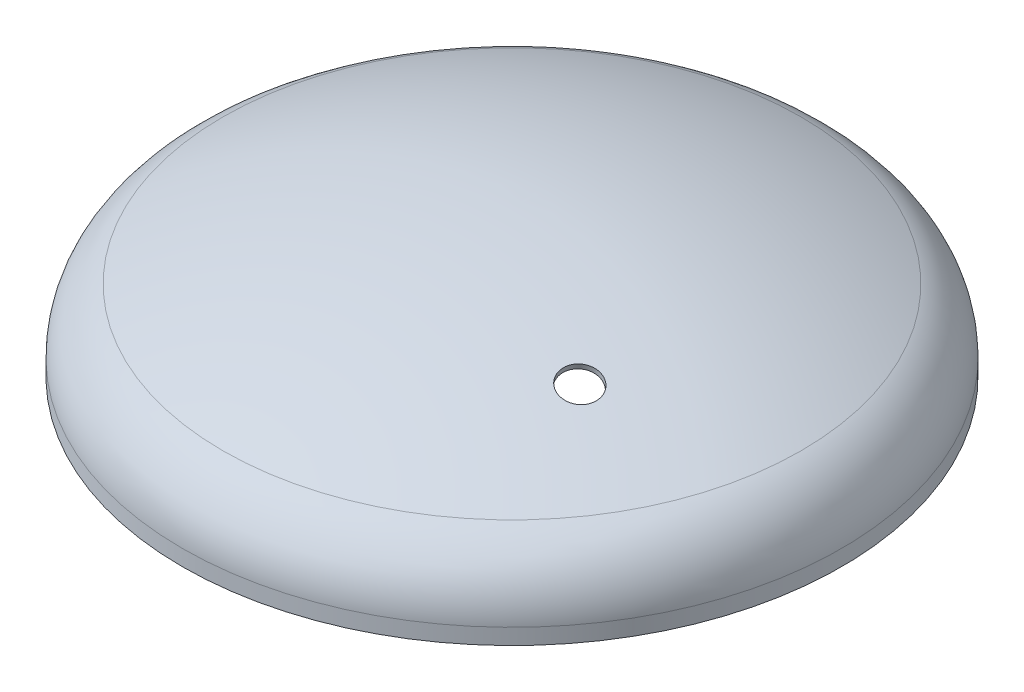
SolidWorks part; units mm, degrees
material "Nichtrostender Chromstahl"
ref_plane "Ebene vorne" through (0, 0, 0) normal (0, 0, 1) x (1, 0, 0)
ref_plane "Ebene oben" through (0, 0, 0) normal (0, 1, 0) x (1, 0, 0)
ref_plane "Ebene rechts" through (0, 0, 0) normal (1, 0, 0) x (0, 0, -1)
sketch "Skizze1" plane through (0, 0, 0) normal (1, 0, 0) x (0, 0, -1)
  line L0 (0, 44.9076) -> (0, -30.8087) construction
  line L1 (177.8, 0) -> (177.8, 8.5377)
  line L2 (174.8, 0) -> (174.8, 8.5377)
  line L3 (174.8, 0) -> (177.8, 0)
  line L4 (0, 79) -> (0, 76)
  arc A0 (155.991, 43.2944) -> (0, 79) centre (0, -279.6) ccw
  arc A1 (177.8, 8.5377) -> (155.991, 43.2944) centre (139.2, 8.5377) ccw
  arc A2 (174.8, 8.5377) -> (154.686, 40.5931) centre (139.2, 8.5377) ccw
  arc A3 (154.686, 40.5931) -> (0, 76) centre (0, -279.6) ccw
  dimension "D2" = 8.5377
  dimension "R1" = 355.6
  dimension "R2" = 35.6
  dimension "H3" = 79
  dimension "D" = 355.6
  dimension "T" = 3
revolve "Rotation1" add sketch "Skizze1" angle 360 about L0
hole_wizard "Ø20.0 (20) Durchmesser Bohrung1" positions "3D-Skizze1" profile "Skizze2" hole size "Ø20.0" standard "DIN"
sketch3d "3D-Skizze1"
  line L0 (0, 0, 0) -> (0, 64.7747, 0) construction
  line L2 (86.6025, 64.7747, 50) -> (0, 64.7747, 0) construction
  line L6 (0, 64.7747, 0) -> (100, 64.7747, 0) construction
  circle A2 centre (0, 64.7747, 0) radius 100
  point P0 (86.6025, 64.7747, 50)
  point P18 (0, 164.7747, 0)
  dimension "D1" = 200
  dimension "D2" = 30
sketch "Skizze2" plane through (86.6025, 64.7747, 50) normal (0.6808, -0.2701, 0.6808) x (-0.6915, 0.0695, 0.719)
  line L0 (0, 0) -> (0, 3)
  line L1 (0, 3) -> (10, 3)
  line L2 (10, 3) -> (10, 0)
  line L5 (10, 0) -> (0, 0)
  line L11 (0, -6.35) -> (0, 107.95) construction
  dimension "Bohrerdurchmesser" = 20
  dimension "Bohrungstiefe" = 3
